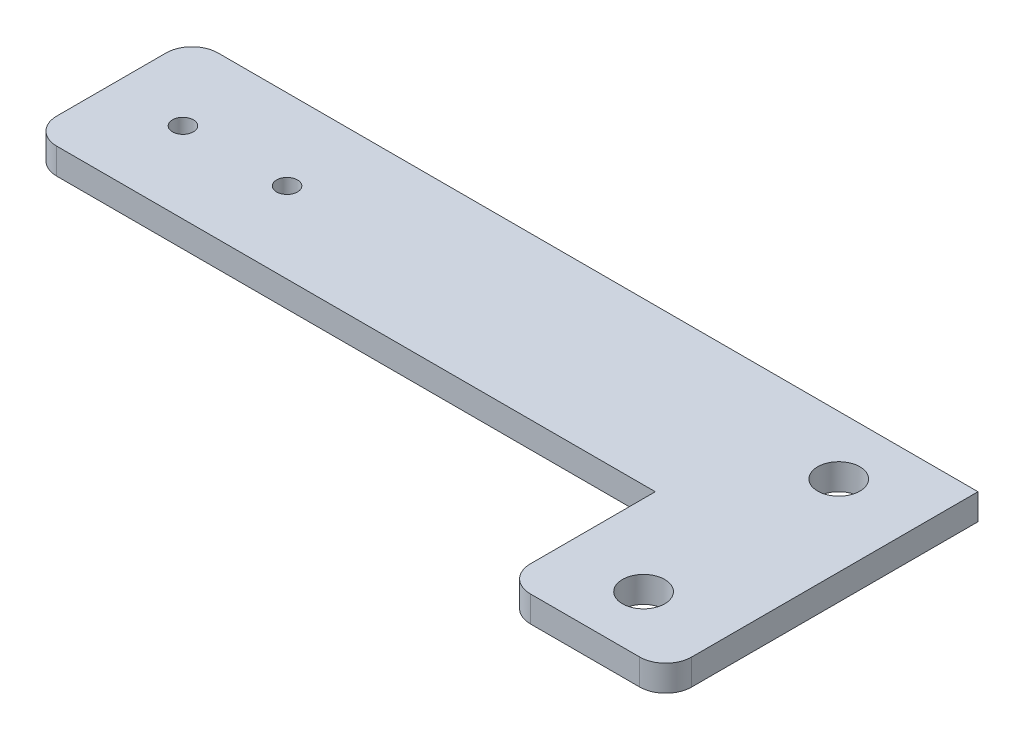
SolidWorks part; units mm, degrees
ref_plane "Front Plane" through (0, 0, 0) normal (0, 0, 1) x (1, 0, 0)
ref_plane "Top Plane" through (0, 0, 0) normal (0, 1, 0) x (1, 0, 0)
ref_plane "Right Plane" through (0, 0, 0) normal (1, 0, 0) x (0, 0, -1)
sketch "Sketch3" plane through (0, 0, 0) normal (0, 1, 0) x (1, 0, 0)
  line L0 (0, 0) -> (191.77, 0)
  line L3 (191.77, 0) -> (191.77, -76.2)
  line L4 (191.77, -76.2) -> (152.4, -76.2)
  line L5 (152.4, -76.2) -> (152.4, -39.37)
  line L6 (152.4, -39.37) -> (0, -39.37)
  line L7 (0, -39.37) -> (0, 0)
  dimension "D1" = 76.2
  dimension "D2" = 152.4
  dimension "D3" = 39.37
extrude "Boss-Extrude1" add sketch "Sketch3" along normal blind 6.35
sketch "Sketch4" plane through (0, 6.35, 0) normal (0, 1, 0) x (1, 0, 0)
  line L0 (152.4, -76.2) -> (191.77, -76.2) construction
  line L1 (152.4, -39.37) -> (152.4, -76.2) construction
  line L2 (0, 0) -> (0, -39.37) construction
  line L3 (152.4, -76.2) -> (191.77, -76.2) construction
  line L4 (60.325, 0) -> (60.325, -39.37) construction
  line L5 (191.77, 0) -> (0, 0) construction
  line L6 (0, -39.37) -> (152.4, -39.37) construction
  line L7 (191.77, -76.2) -> (191.77, 0) construction
  line L8 (191.77, 0) -> (0, 0) construction
  line L9 (152.4, -76.2) -> (152.4, 0) construction
  line L10 (172.085, -61.9125) -> (172.085, -14.2875) construction
  line L11 (17.4625, -19.685) -> (42.8625, -19.685) construction
  line L12 (0, -39.37) -> (60.325, -39.37)
  circle A0 centre (17.4625, -19.685) radius 2.5527
  circle A1 centre (42.8625, -19.685) radius 2.5527
  circle A4 centre (172.085, -14.2875) radius 5.1562
  circle A5 centre (172.085, -61.9125) radius 5.1562
  point P8 (172.085, -76.2)
  point P16 (0, -19.685)
  point P29 (152.4, -38.1)
  point P30 (172.085, -38.1)
  point P34 (30.1625, -39.37)
  point P35 (30.1625, -19.685)
  dimension "D1" = 5.1054
  dimension "D2" = 10.3124
  dimension "D3" = 47.625
  dimension "D4" = 60.325
  dimension "D5" = 76.2
  dimension "D6" = 25.4
extrude "Cut-Extrude1" cut sketch "Sketch4" against normal up to next contours A0 | A1 | A4 | A5
fillet "Fillet1" radius 6.35 4 edges at (0, 3.175, 0) (191.77, 3.175, 76.2) (152.4, 3.175, 76.2) (0, 3.175, 39.37)
